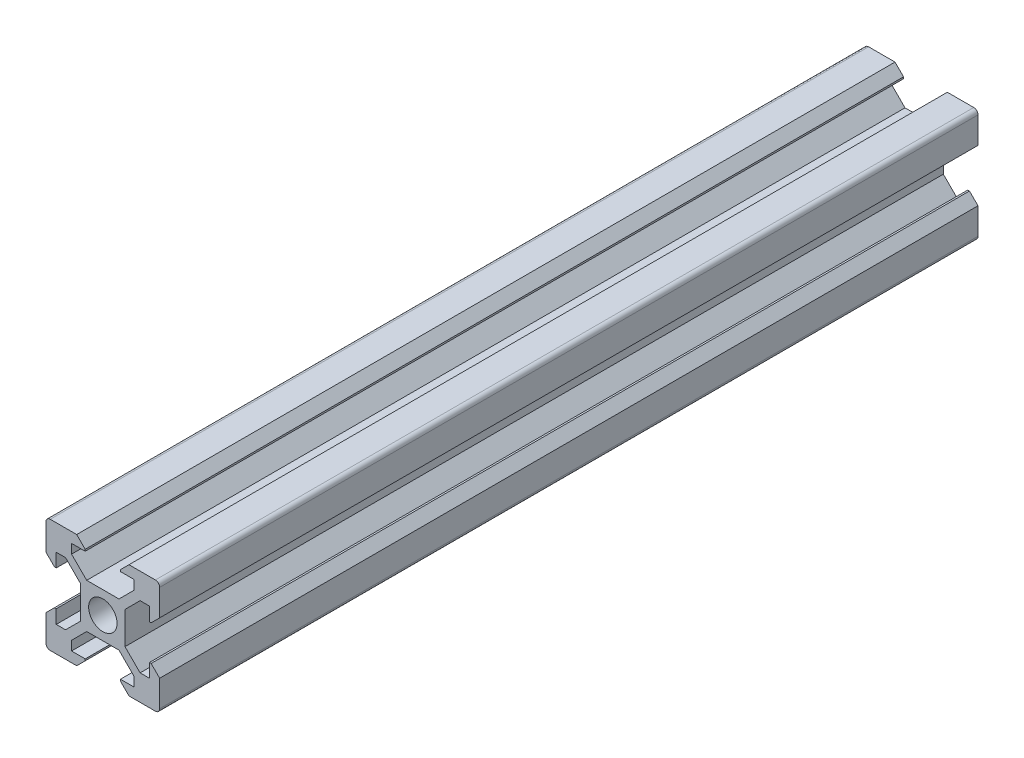
SolidWorks part; units mm, degrees
other "Markup1"
sketch "Sketch1" plane through (10, 10, 480) normal (0.5774, 0.5773, 0.5774) x (0.7071, 0, -0.7071)
ref_plane "Alzado" through (0, 0, 0) normal (0, 0, 1) x (1, 0, 0)
ref_plane "Planta" through (0, 0, 0) normal (0, 1, 0) x (1, 0, 0)
ref_plane "Vista lateral" through (0, 0, 0) normal (1, 0, 0) x (0, 0, -1)
sketch "Croquis1" plane through (0, 0, 0) normal (0, 0, 1) x (1, 0, 0)
  line L0 (-4.6, 10) -> (-3.1, 8.5)
  line L3 (-4.6, 10) -> (-9.25, 10)
  line L5 (-3.1, 8.5) -> (-3.1, 8.2)
  line L6 (-3.1, 8.2) -> (-5.5, 8.2)
  line L7 (-5.5, 8.2) -> (-5.5, 6.5607)
  line L8 (-5.5, 6.5607) -> (-2.84, 3.9007)
  line L9 (-2.84, 3.9007) -> (0, 3.9007)
  line L10 (0, 0) -> (-15.3499, 15.3499) construction
  line L11 (-3.9007, 2.84) -> (-3.9007, 0)
  line L12 (-6.5607, 5.5) -> (-3.9007, 2.84)
  line L13 (-8.2, 5.5) -> (-6.5607, 5.5)
  line L14 (-8.2, 3.1) -> (-8.2, 5.5)
  line L15 (-8.5, 3.1) -> (-8.2, 3.1)
  line L16 (-10, 4.6) -> (-10, 9.25)
  line L17 (-10, 4.6) -> (-8.5, 3.1)
  line L18 (10, 4.6) -> (8.5, 3.1)
  line L19 (10, 4.6) -> (10, 9.25)
  line L20 (8.5, 3.1) -> (8.2, 3.1)
  line L21 (8.2, 3.1) -> (8.2, 5.5)
  line L22 (8.2, 5.5) -> (6.5607, 5.5)
  line L23 (6.5607, 5.5) -> (3.9007, 2.84)
  line L24 (3.9007, 2.84) -> (3.9007, 0)
  line L25 (5.5, 6.5607) -> (2.84, 3.9007)
  line L26 (5.5, 8.2) -> (5.5, 6.5607)
  line L27 (3.1, 8.2) -> (5.5, 8.2)
  line L28 (3.1, 8.5) -> (3.1, 8.2)
  line L29 (4.6, 10) -> (9.25, 10)
  line L30 (4.6, 10) -> (3.1, 8.5)
  line L31 (2.84, 3.9007) -> (0, 3.9007)
  line L32 (4.6, -10) -> (3.1, -8.5)
  line L33 (4.6, -10) -> (9.25, -10)
  line L34 (3.1, -8.5) -> (3.1, -8.2)
  line L35 (3.1, -8.2) -> (5.5, -8.2)
  line L36 (5.5, -8.2) -> (5.5, -6.5607)
  line L37 (5.5, -6.5607) -> (2.84, -3.9007)
  line L38 (2.84, -3.9007) -> (0, -3.9007)
  line L39 (6.5607, -5.5) -> (3.9007, -2.84)
  line L40 (8.2, -5.5) -> (6.5607, -5.5)
  line L41 (8.2, -3.1) -> (8.2, -5.5)
  line L42 (8.5, -3.1) -> (8.2, -3.1)
  line L43 (10, -4.6) -> (10, -9.25)
  line L44 (10, -4.6) -> (8.5, -3.1)
  line L45 (3.9007, -2.84) -> (3.9007, 0)
  line L46 (-10, -4.6) -> (-8.5, -3.1)
  line L47 (-10, -4.6) -> (-10, -9.25)
  line L48 (-8.5, -3.1) -> (-8.2, -3.1)
  line L49 (-8.2, -3.1) -> (-8.2, -5.5)
  line L50 (-8.2, -5.5) -> (-6.5607, -5.5)
  line L51 (-6.5607, -5.5) -> (-3.9007, -2.84)
  line L52 (-3.9007, -2.84) -> (-3.9007, 0)
  line L53 (-5.5, -6.5607) -> (-2.84, -3.9007)
  line L54 (-5.5, -8.2) -> (-5.5, -6.5607)
  line L55 (-3.1, -8.2) -> (-5.5, -8.2)
  line L56 (-3.1, -8.5) -> (-3.1, -8.2)
  line L57 (-4.6, -10) -> (-9.25, -10)
  line L58 (-4.6, -10) -> (-3.1, -8.5)
  line L59 (-2.84, -3.9007) -> (0, -3.9007)
  circle A0 centre (0, 0) radius 2.5
  arc A1 (-9.25, 10) -> (-10, 9.25) centre (-9.25, 9.25) ccw
  arc A2 (10, 9.25) -> (9.25, 10) centre (9.25, 9.25) ccw
  arc A3 (9.25, -10) -> (10, -9.25) centre (9.25, -9.25) ccw
  arc A4 (-10, -9.25) -> (-9.25, -10) centre (-9.25, -9.25) ccw
  point P18 (-10, 10)
  point P37 (10, 10)
  point P55 (10, -10)
  point P73 (-10, -10)
  point P79 (0, 0)
  dimension "D1" = 5
  dimension "D5" = 0.75
  dimension "D2" = 10
  dimension "D3" = 10
  dimension "D4" = 4.6
  dimension "D6" = 5.5
  dimension "D7" = 135
  dimension "D8" = 0.75
  dimension "D9" = 225
  dimension "D10" = 2.84
  dimension "D11" = 1.8
  dimension "D12" = 3.1
  dimension "D13" = 4
extrude "Saliente-Extruir1" add sketch "Croquis1" along normal blind 144
